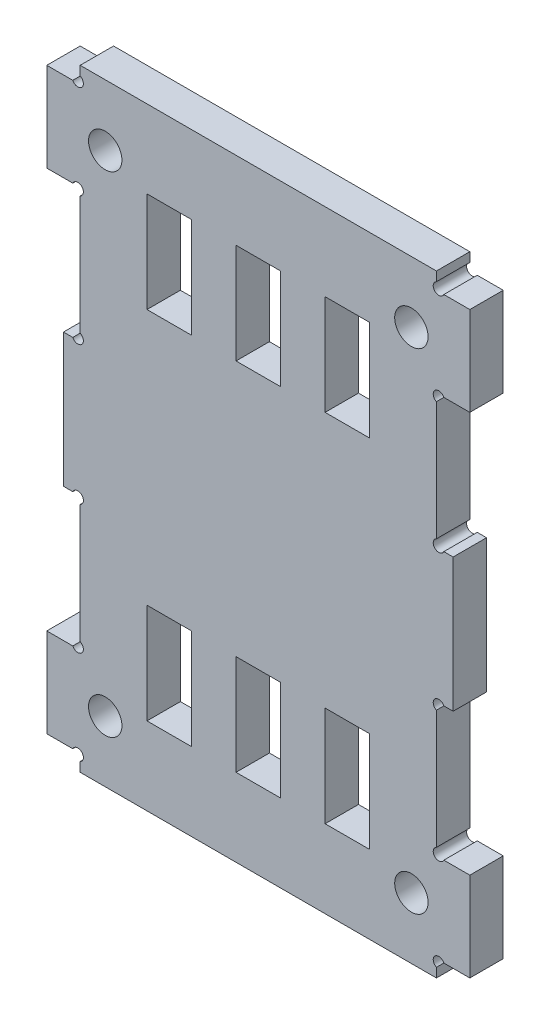
SolidWorks part; units mm, degrees
ref_plane "前视基准面" through (0, 0, 0) normal (0, 0, 1) x (1, 0, 0)
ref_plane "上视基准面" through (0, 0, 0) normal (0, 1, 0) x (1, 0, 0)
ref_plane "右视基准面" through (0, 0, 0) normal (1, 0, 0) x (0, 0, -1)
sketch "草图1" plane through (0, 0, 0) normal (0, 0, 1) x (1, 0, 0)
  line L1 (-19, 27.5) -> (19, 27.5)
  line L2 (-19, 27.5) -> (-19, -27.5)
  line L3 (-19, -27.5) -> (19, -27.5)
  line L4 (19, 27.5) -> (19, -27.5)
  line L5 (-19, 27.5) -> (19, -27.5) construction
  line L6 (-19, -27.5) -> (19, 27.5) construction
  point P0 (0, 0)
  dimension "D1" = 55
  dimension "D2" = 38
extrude "凸台-拉伸1" add sketch "草图1" along normal blind 3
sketch "草图2" plane through (0, 0, 3) normal (0, 0, 1) x (1, 0, 0)
  line L0 (0, -31.2888) -> (0, 37.0757) construction
  line L1 (-24.0306, 0) -> (34.3294, 0) construction
  line L2 (-19, 27.5) -> (-19, -27.5) construction
  line L3 (-19, -26) -> (-16, -26) construction
  line L4 (-19, -26) -> (-19, -18) construction
  line L5 (-19, -18) -> (-16, -18) construction
  line L6 (-16, -26) -> (-16, -18) construction
  line L7 (-16, -27.5) -> (-16, -26)
  line L8 (-19, -27.5) -> (19, -27.5) construction
  line L9 (-16, -26) -> (-19, -26)
  line L10 (-19, -26) -> (-19, -18)
  line L11 (-19, -18) -> (-16, -18)
  line L12 (-16, -18) -> (-16, 18)
  line L13 (-19, 18) -> (-16, 18)
  line L14 (-19, 26) -> (-19, 18)
  line L15 (-16, 26) -> (-19, 26)
  line L16 (-16, 27.5) -> (-16, 26)
  line L17 (16, -26) -> (16, -18) construction
  line L18 (19, -18) -> (16, -18) construction
  line L19 (19, -26) -> (19, -18) construction
  line L20 (19, -26) -> (16, -26) construction
  line L21 (19, 27.5) -> (16, 27.5)
  line L22 (19, 26) -> (19, 27.5)
  line L23 (19, -18) -> (19, 18)
  line L24 (19, -27.5) -> (19, -26)
  line L25 (16, -27.5) -> (19, -27.5)
  line L26 (16, 27.5) -> (16, 26)
  line L27 (16, 26) -> (19, 26)
  line L28 (19, 26) -> (19, 18)
  line L29 (19, 18) -> (16, 18)
  line L30 (-16, -27.5) -> (-19, -27.5)
  line L31 (-19, -27.5) -> (-19, -26)
  line L32 (-19, -18) -> (-19, 18)
  line L33 (-19, 26) -> (-19, 27.5)
  line L34 (-19, 27.5) -> (-16, 27.5)
  line L35 (16, -18) -> (16, 18)
  line L36 (19, -18) -> (16, -18)
  line L37 (19, -26) -> (19, -18)
  line L38 (16, -26) -> (19, -26)
  line L39 (16, -27.5) -> (16, -26)
  point P16 (-16, 0)
  point P36 (16, 0)
  point P37 (-17.5, -26)
  line M10 (19, -27.5) -> (19, 27.5)
  line M11 (19, 27.5) -> (-19, 27.5)
  line M12 (-19, 27.5) -> (-19, -27.5)
  line M13 (-19, -27.5) -> (19, -27.5)
  dimension "D1" = 1.5
  dimension "D2" = 8
  dimension "D3" = 3
extrude "切除-拉伸1" cut sketch "草图2" against normal blind 3 contours L13 L11 L12 M12 | L16 L15 M11 M12 | L39 L38 M13 M10 | L36 L29 L35 M10 | L26 L27 M10 M11 | L9 L7 L30 L31
sketch "草图3" plane through (0, 0, 3) normal (0, 0, 1) x (1, 0, 0)
  line L0 (0, -30.3674) -> (0, 32.2406) construction
  line L1 (-19.4107, 0) -> (21.9704, 0) construction
  line L2 (-19, -18) -> (-19, -26) construction
  circle A0 centre (-13.75, -22) radius 1.5
  circle A1 centre (13.75, -22) radius 1.5
  circle A2 centre (13.75, 22) radius 1.5
  circle A3 centre (-13.75, 22) radius 1.5
  point P10 (-19, -22)
  dimension "D1" = 13.75
  dimension "D2" = 3
extrude "切除-拉伸2" cut sketch "草图3" against normal through all
sketch "草图4" plane through (0, 0, 3) normal (0, 0, 1) x (1, 0, 0)
  line L0 (-14, -16) -> (14, -16) construction
  line L1 (6, -20.5) -> (6, -11.5)
  line L2 (-2, -20.5) -> (2, -20.5)
  line L3 (-2, -20.5) -> (-2, -11.5)
  line L4 (-2, -11.5) -> (2, -11.5)
  line L5 (2, -20.5) -> (2, -11.5)
  line L6 (-2, -20.5) -> (2, -11.5) construction
  line L7 (-2, -11.5) -> (2, -20.5) construction
  line L8 (6, -20.5) -> (10, -20.5)
  line L9 (10, -20.5) -> (10, -11.5)
  line L10 (6, -11.5) -> (10, -11.5)
  line L11 (-10, -20.5) -> (-10, -11.5)
  line L12 (-10, -20.5) -> (-6, -20.5)
  line L13 (-6, -20.5) -> (-6, -11.5)
  line L14 (-10, -11.5) -> (-6, -11.5)
  line L15 (-21.1994, 0) -> (24.8064, 0) construction
  line L16 (-2, 11.5) -> (2, 20.5) construction
  line L17 (-2, 20.5) -> (2, 11.5) construction
  line L18 (-10, 11.5) -> (-6, 11.5)
  line L19 (-6, 20.5) -> (-6, 11.5)
  line L20 (-10, 20.5) -> (-6, 20.5)
  line L21 (-10, 20.5) -> (-10, 11.5)
  line L22 (6, 11.5) -> (10, 11.5)
  line L23 (10, 20.5) -> (10, 11.5)
  line L24 (6, 20.5) -> (10, 20.5)
  line L25 (2, 20.5) -> (2, 11.5)
  line L26 (-2, 11.5) -> (2, 11.5)
  line L27 (-2, 20.5) -> (-2, 11.5)
  line L28 (-2, 20.5) -> (2, 20.5)
  line L29 (6, 20.5) -> (6, 11.5)
  point P4 (0, -16)
  point P32 (0, 16)
  dimension "D1" = 4
  dimension "D2" = 2
  dimension "D3" = 9
  dimension "D4" = 2
  dimension "D5" = 32
extrude "切除-拉伸3" cut sketch "草图4" against normal blind 10
sketch "草图5" plane through (0, 0, 3) normal (0, 0, 1) x (1, 0, 0)
  line L0 (-16, -18) -> (-16, 18) construction
  line L1 (-17.5, -6) -> (-16, -6)
  line L2 (-17.5, -6) -> (-17.5, 6)
  line L3 (-17.5, 6) -> (-16, 6)
  line L4 (-16, -6) -> (-16, 6)
  line L5 (-17.5, -6) -> (-16, 6) construction
  line L6 (-17.5, 6) -> (-16, -6) construction
  line L7 (0, -53.1922) -> (0, 41.3599) construction
  line L8 (16, -18) -> (16, 18) construction
  line L9 (17.5, 6) -> (16, 6)
  line L10 (17.5, 6) -> (17.5, -6)
  line L11 (17.5, -6) -> (16, -6)
  line L12 (16, 6) -> (16, -6)
  line L13 (17.5, 6) -> (16, -6) construction
  line L14 (17.5, -6) -> (16, 6) construction
  point P0 (-16.75, 0)
  point P11 (16.75, 0)
  point P15 (16.75, 0)
  dimension "D1" = 12
  dimension "D2" = 1.5
  dimension "D3" = 12
  dimension "D4" = 1.5
extrude "凸台-拉伸2" add sketch "草图5" against normal through all
sketch "草图6" plane through (0, 0, 3) normal (0, 0, 1) x (1, 0, 0)
  line L0 (-16, -26) -> (-17.6148, -27.6148) construction
  line L1 (-16, -27.5) -> (-16, -26) construction
  line L2 (-23.8038, 0) -> (24.1054, 0) construction
  line L3 (0, -33.8232) -> (0, 34.4969) construction
  line L4 (-19, -22) -> (-12.25, -22) construction
  line L5 (-19, -18) -> (-19, -26) construction
  line L6 (-16, -12) -> (16, -12) construction
  line L7 (-16, -18) -> (-16, -6) construction
  line L8 (16, -18) -> (16, -6) construction
  line L9 (-16, 26) -> (-17.6148, 27.6148) construction
  circle A0 centre (-16.2121, -26.2121) radius 0.5
  circle A1 centre (-13.75, -22) radius 1.5 construction
  circle A2 centre (-16.2121, -17.7879) radius 0.5
  circle A3 centre (-16.2121, -6.2121) radius 0.5
  circle A4 centre (16.2121, -6.2121) radius 0.5
  circle A5 centre (16.2121, -17.7879) radius 0.5
  circle A6 centre (16.2121, -26.2121) radius 0.5
  circle A7 centre (16.2121, 26.2121) radius 0.5
  circle A8 centre (16.2121, 17.7879) radius 0.5
  circle A9 centre (16.2121, 6.2121) radius 0.5
  circle A10 centre (-16.2121, 6.2121) radius 0.5
  circle A11 centre (-16.2121, 17.7879) radius 0.5
  circle A12 centre (-16.2121, 26.2121) radius 0.5
  dimension "D1" = 45
  dimension "D2" = 1
  dimension "D3" = 0.3
extrude "切除-拉伸4" cut sketch "草图6" against normal blind 10
